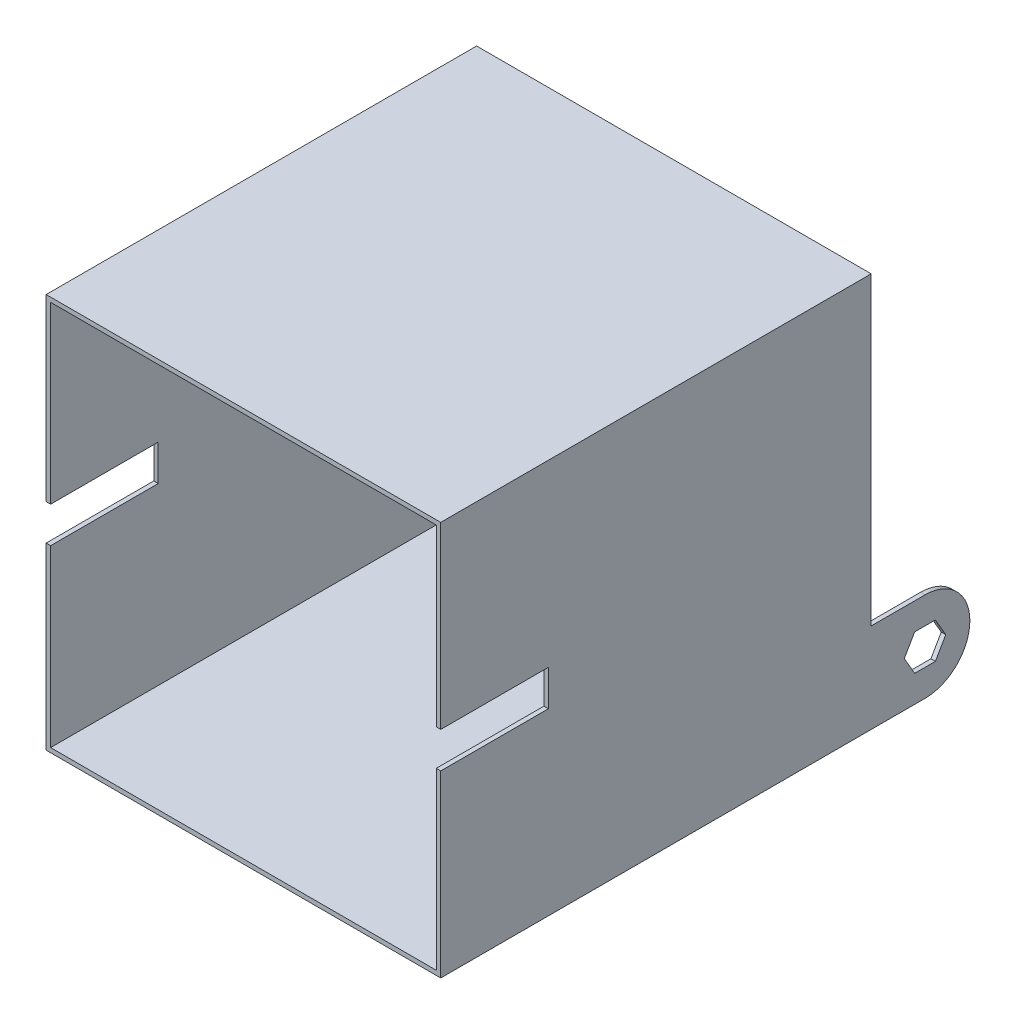
SolidWorks part; units mm, degrees
ref_plane "Front Plane" through (0, 0, 0) normal (0, 0, 1) x (1, 0, 0)
ref_plane "Top Plane" through (0, 0, 0) normal (0, 1, 0) x (1, 0, 0)
ref_plane "Right Plane" through (0, 0, 0) normal (1, 0, 0) x (0, 0, -1)
sketch "Sketch2" plane through (0, 0, 0) normal (0, 0, 1) x (1, 0, 0)
  line L1 (0, 0) -> (279.4, 0)
  line L2 (0, 0) -> (0, 279.4)
  line L3 (0, 279.4) -> (279.4, 279.4)
  line L4 (279.4, 0) -> (279.4, 279.4)
  dimension "D1" = 279.4
extrude "Boss-Extrude2" add sketch "Sketch2" along normal blind 304.8
shell "Shell2" thickness 3.175
sketch "Sketch4" plane through (0, 0, 0) normal (-1, 0, 0) x (0, 0, 1)
  line L0 (304.8, 279.4) -> (304.8, 0) construction
  line L1 (228.6, 152.4) -> (304.8, 152.4)
  line L2 (228.6, 152.4) -> (228.6, 127)
  line L3 (228.6, 127) -> (304.8, 127)
  line L4 (304.8, 152.4) -> (304.8, 127)
  line L5 (304.8, 279.4) -> (0, 279.4) construction
  dimension "D1" = 127
  dimension "D2" = 25.4
  dimension "D3" = 76.2
extrude "Cut-Extrude2" cut sketch "Sketch4" against normal through all
sketch "Sketch5" plane through (279.4, 0, 0) normal (1, 0, 0) x (0, 0, -1)
  line L0 (0, 0) -> (0, 279.4) construction
  line L2 (0, 0) -> (38.1, 0)
  line L3 (23.4353, 31.75) -> (30.7677, 19.05)
  line L4 (30.7677, 19.05) -> (45.4323, 19.05)
  line L5 (45.4323, 19.05) -> (52.7647, 31.75)
  line L6 (52.7647, 31.75) -> (45.4323, 44.45)
  line L7 (45.4323, 44.45) -> (30.7677, 44.45)
  line L8 (30.7677, 44.45) -> (23.4353, 31.75)
  line L9 (38.1, 0) -> (38.1, 63.5)
  line L10 (38.1, 63.5) -> (0, 63.5)
  arc A0 (38.1, 0) -> (38.1, 63.5) centre (38.1, 31.75) ccw
  circle A1 centre (38.1, 31.75) radius 12.7 construction
  line M7 (0, 0) -> (0, 279.4)
  dimension "D1" = 63.5
  dimension "D2" = 38.1
  dimension "D3" = 31.75
  dimension "D4" = 25.4
extrude "Boss-Extrude5" add sketch "Sketch5" against normal blind 3.175 contours L9 L10 L2 L4 L3 L8 L7 M7 | L9 A0 L7 L6 L5 L4
ref_plane "Plane3" through (139.7, 0, 0) normal (1, 0, 0) x (0, 0, -1)
mirror "Mirror1" about plane through (139.7, 0, 0) normal (1, 0, 0) of "Boss-Extrude5"
sketch "Sketch6" plane through (0, 0, 0) normal (0, 0, -1) x (-1, 0, 0)
  circle A0 centre (-139.7, 139.7) radius 12.7
  dimension "D3" = 25.4
  dimension "D1" = 139.7
  dimension "D2" = 139.7
extrude "Cut-Extrude3" cut sketch "Sketch6" against normal through all
